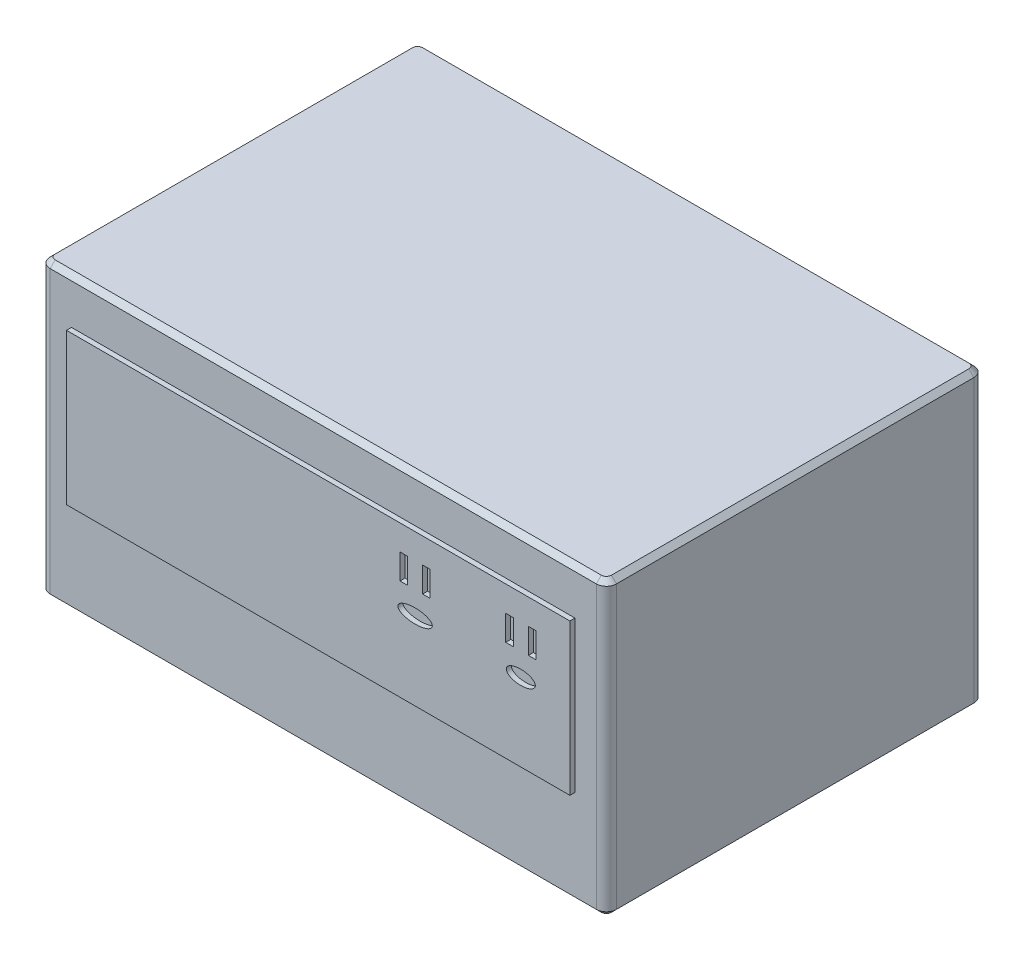
SolidWorks part; units mm, degrees
ref_plane "Front Plane" through (0, 0, 0) normal (0, 0, 1) x (1, 0, 0)
ref_plane "Top Plane" through (0, 0, 0) normal (0, 1, 0) x (1, 0, 0)
ref_plane "Right Plane" through (0, 0, 0) normal (1, 0, 0) x (0, 0, -1)
sketch "Sketch1" plane through (0, 0, 0) normal (0, 1, 0) x (1, 0, 0)
  line L1 (-142.875, 76.0996) -> (142.875, 76.0996)
  line L2 (-142.875, 76.0996) -> (-142.875, -114.4004)
  line L3 (-142.875, -114.4004) -> (142.875, -114.4004)
  line L4 (142.875, 76.0996) -> (142.875, -114.4004)
  line L5 (-142.875, 76.0996) -> (142.875, -114.4004) construction
  line L6 (-142.875, -114.4004) -> (142.875, 76.0996) construction
  point P0 (0, -19.1504)
  dimension "D1" = 285.75
  dimension "D2" = 190.5
extrude "Boss-Extrude1" add sketch "Sketch1" along normal blind 147.32
sketch "Sketch2" plane through (0, 0, 114.4004) normal (0, 0, 1) x (1, 0, 0)
  line L1 (-127, 124.46) -> (127, 124.46)
  line L2 (-127, 124.46) -> (-127, 48.26)
  line L3 (-127, 48.26) -> (127, 48.26)
  line L4 (127, 124.46) -> (127, 48.26)
  line L5 (-142.875, 0) -> (142.875, 0) construction
  line L7 (-142.875, 147.32) -> (-142.875, 0) construction
  dimension "D1" = 254
  dimension "D2" = 15.875
  dimension "D3" = 76.2
  dimension "D4" = 48.26
extrude "Boss-Extrude2" add sketch "Sketch2" along normal blind 2.54
sketch "Sketch3" plane through (0, 0, 116.9404) normal (0, 0, 1) x (1, 0, 0)
  line L1 (41.275, 111.76) -> (45.085, 111.76)
  line L2 (41.275, 111.76) -> (41.275, 99.06)
  line L3 (41.275, 99.06) -> (45.085, 99.06)
  line L4 (45.085, 111.76) -> (45.085, 99.06)
  line L10 (52.705, 111.76) -> (56.515, 111.76)
  line L11 (52.705, 111.76) -> (52.705, 99.06)
  line L12 (52.705, 99.06) -> (56.515, 99.06)
  line L13 (56.515, 111.76) -> (56.515, 99.06)
  line L14 (94.615, 111.6275) -> (98.425, 111.6275)
  line L15 (94.615, 111.6275) -> (94.615, 98.9275)
  line L16 (94.615, 98.9275) -> (98.425, 98.9275)
  line L17 (98.425, 111.6275) -> (98.425, 98.9275)
  line L18 (106.045, 111.6275) -> (109.855, 111.6275)
  line L19 (106.045, 111.6275) -> (106.045, 98.9275)
  line L20 (106.045, 98.9275) -> (109.855, 98.9275)
  line L21 (109.855, 111.6275) -> (109.855, 98.9275)
  line L23 (142.875, 147.32) -> (142.875, 0) construction
  ellipse E0 centre (48.895, 87.5876) end of major axis (57.5647, 87.5876) minor radius 3.5533
  ellipse E1 centre (102.235, 87.4552) end of major axis (109.5566, 87.4552) minor radius 3.5533
  point P6 (0, 0)
  point P14 (77.404, 82.015)
  point P20 (67.6084, 82.015)
  point P21 (0, 0)
  point P22 (74.93, 78.4617)
  point P23 (0, 0)
  point P24 (0, 0)
  dimension "D1" = 3.81
  dimension "D2" = 12.7
  dimension "D3" = 101.6
  dimension "D4" = 3.81
  dimension "D5" = 3.81
  dimension "D6" = 12.7
  dimension "D7" = 7.62
  dimension "D8" = 3.81
  dimension "D10" = 3.81
  dimension "D11" = 12.7
  dimension "D12" = 3.81
  dimension "D13" = 12.7
  dimension "D14" = 7.62
  dimension "D15" = 38.1
extrude "Cut-Extrude1" cut sketch "Sketch3" against normal blind 2.54 contours L4 L1 L2 L3 | L13 L10 L11 L12 | E0 | E1 | L17 L14 L15 L16 | L21 L18 L19 L20
fillet "Fillet1" radius 5.08 4 edges at (-142.875, 73.66, -76.0996) (-142.875, 73.66, 114.4004) (142.875, 73.66, -76.0996) (142.875, 73.66, 114.4004)
chamfer "Chamfer1" distance 2.54 angle 45 16 edges at (0, 0, -76.0996) (-141.3871, 0, -74.6117) (141.3871, 0, -74.6117) (-142.875, 0, 19.1504) (142.875, 0, 19.1504) (-141.3871, 0, 112.9125) (141.3871, 0, 112.9125) (0, 0, 114.4004) (-142.875, 147.32, 19.1504) (0, 147.32, -76.0996) (142.875, 147.32, 19.1504) (-141.3871, 147.32, -74.6117) (141.3871, 147.32, -74.6117) (-141.3871, 147.32, 112.9125) (141.3871, 147.32, 112.9125) (0, 147.32, 114.4004)
